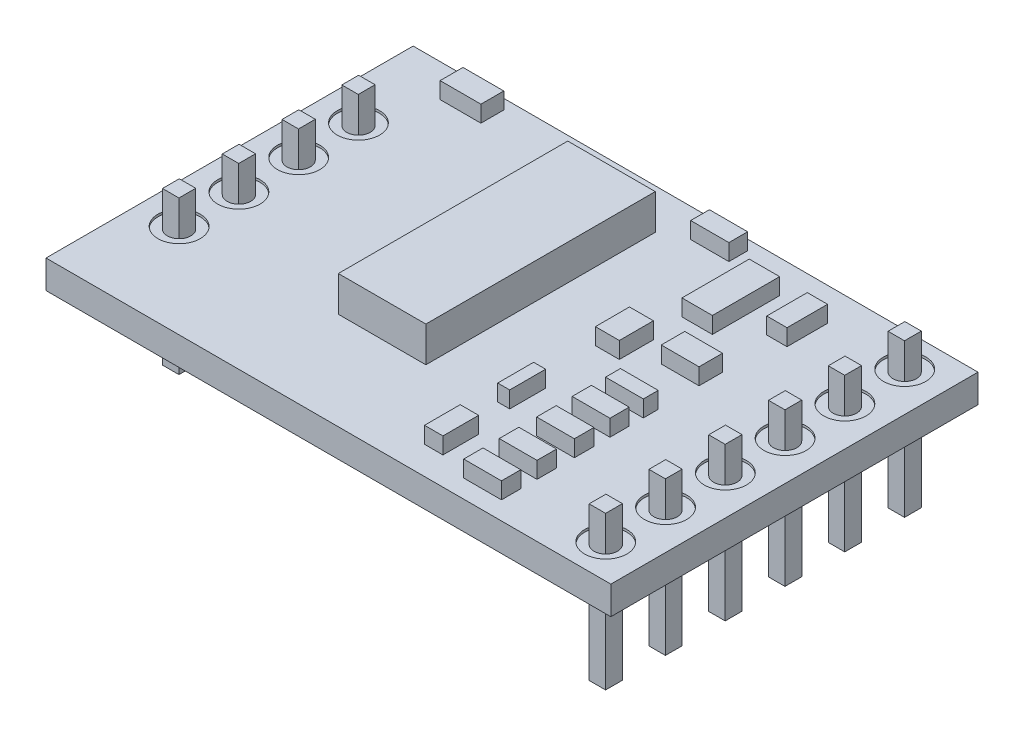
SolidWorks part; units mm, degrees
ref_plane "Front Plane" through (0, 0, 0) normal (0, 0, 1) x (1, 0, 0)
ref_plane "Top Plane" through (0, 0, 0) normal (0, 1, 0) x (1, 0, 0)
ref_plane "Right Plane" through (0, 0, 0) normal (1, 0, 0) x (0, 0, -1)
sketch "Sketch1" plane through (0, 0, 0) normal (0, 1, 0) x (1, 0, 0)
  line L1 (-12, -7.8) -> (12, -7.8)
  line L2 (-12, -7.8) -> (-12, 7.8)
  line L3 (-12, 7.8) -> (12, 7.8)
  line L4 (12, -7.8) -> (12, 7.8)
  line L5 (-12, -7.8) -> (12, 7.8) construction
  line L6 (-12, 7.8) -> (12, -7.8) construction
  point P0 (0, 0)
  dimension "D1" = 24
  dimension "D2" = 15.6
extrude "Boss-Extrude1" add sketch "Sketch1" along normal blind 1.2
sketch "Sketch3" plane through (0, 1.2, 0) normal (0, 1, 0) x (1, 0, 0)
  line L1 (-3.7188, 6.0872) -> (0, 6.0872)
  line L2 (-3.7188, 6.0872) -> (-3.7188, -3.6601)
  line L3 (-3.7188, -3.6601) -> (0, -3.6601)
  line L4 (0, 6.0872) -> (0, -3.6601)
extrude "Boss-Extrude2" add sketch "Sketch3" along normal blind 1.5
sketch "Sketch4" plane through (0, 1.2, 0) normal (0, 1, 0) x (1, 0, 0)
  line L1 (3.6797, 6.4003) -> (4.9715, 6.4003)
  line L2 (3.6797, 6.4003) -> (3.6797, 3.5427)
  line L3 (3.6797, 3.5427) -> (4.9715, 3.5427)
  line L4 (4.9715, 6.4003) -> (4.9715, 3.5427)
  line L5 (6.1459, 6.4003) -> (7.0071, 6.4003)
  line L6 (6.1459, 6.4003) -> (6.1459, 4.6779)
  line L7 (6.1459, 4.6779) -> (7.0071, 4.6779)
  line L8 (7.0071, 6.4003) -> (7.0071, 4.6779)
  line L9 (2.8968, 2.0943) -> (3.9146, 2.0943)
  line L10 (2.8968, 2.0943) -> (2.8968, 0.6459)
  line L11 (2.8968, 0.6459) -> (3.9146, 0.6459)
  line L12 (3.9146, 2.0943) -> (3.9146, 0.6459)
  line L13 (4.9715, 2.3683) -> (6.5765, 2.3683)
  line L14 (4.9715, 2.3683) -> (4.9715, 1.3701)
  line L15 (4.9715, 1.3701) -> (6.5765, 1.3701)
  line L16 (6.5765, 2.3683) -> (6.5765, 1.3701)
  line L17 (2.8968, -1.9769) -> (3.4057, -1.9769)
  line L18 (2.8968, -1.9769) -> (2.8968, -3.5035)
  line L19 (2.8968, -3.5035) -> (3.4057, -3.5035)
  line L20 (3.4057, -1.9769) -> (3.4057, -3.5035)
  line L21 (4.9715, -0.3642) -> (6.5765, -0.3642)
  line L22 (4.9715, -0.3642) -> (4.9715, -0.9964)
  line L23 (4.9715, -0.9964) -> (6.5765, -0.9964)
  line L24 (6.5765, -0.3642) -> (6.5765, -0.9964)
  line L25 (4.9715, -1.5977) -> (6.5765, -1.5977)
  line L26 (4.9715, -1.5977) -> (4.9715, -2.415)
  line L27 (4.9715, -2.415) -> (6.5765, -2.415)
  line L28 (6.5765, -1.5977) -> (6.5765, -2.415)
  line L29 (4.9715, -3.0934) -> (6.5765, -3.0934)
  line L30 (4.9715, -3.0934) -> (4.9715, -3.9261)
  line L31 (4.9715, -3.9261) -> (6.5765, -3.9261)
  line L32 (6.5765, -3.0934) -> (6.5765, -3.9261)
  line L33 (4.9715, -4.6817) -> (6.5765, -4.6817)
  line L34 (4.9715, -4.6817) -> (4.9715, -5.5143)
  line L35 (4.9715, -5.5143) -> (6.5765, -5.5143)
  line L36 (6.5765, -4.6817) -> (6.5765, -5.5143)
  line L37 (4.9715, -6.2045) -> (6.5765, -6.2045)
  line L38 (4.9715, -6.2045) -> (4.9715, -7.0239)
  line L39 (4.9715, -7.0239) -> (6.5765, -7.0239)
  line L40 (6.5765, -6.2045) -> (6.5765, -7.0239)
  line L41 (2.8968, -5.098) -> (3.6797, -5.098)
  line L42 (2.8968, -5.098) -> (2.8968, -6.6142)
  line L43 (2.8968, -6.6142) -> (3.6797, -6.6142)
  line L44 (3.6797, -5.098) -> (3.6797, -6.6142)
  line L45 (1.0168, 7.3718) -> (2.6398, 7.3718)
  line L46 (1.0168, 7.3718) -> (1.0168, 6.575)
  line L47 (1.0168, 6.575) -> (2.6398, 6.575)
  line L48 (2.6398, 7.3718) -> (2.6398, 6.575)
  line L49 (-9.4546, 7.3718) -> (-7.7209, 7.3718)
  line L50 (-9.4546, 7.3718) -> (-9.4546, 6.4003)
  line L51 (-9.4546, 6.4003) -> (-7.7209, 6.4003)
  line L52 (-7.7209, 7.3718) -> (-7.7209, 6.4003)
extrude "Boss-Extrude3" add sketch "Sketch4" along normal blind 0.7
sketch "Sketch5" plane through (0, 1.2, 0) normal (0, 1, 0) x (1, 0, 0)
  line L0 (-10.3345, 7.8) -> (-10.3345, -7.8) construction
  line L1 (12, 7.8) -> (-12, 7.8) construction
  line L2 (-12, -7.8) -> (12, -7.8) construction
  line L3 (0, 0) -> (0, -7.8) construction
  circle A0 centre (-10.3345, 3.81) radius 0.5
  circle A1 centre (-10.3345, 1.27) radius 0.5
  circle A2 centre (-10.3345, -1.27) radius 0.5
  circle A3 centre (-10.3345, -3.81) radius 0.5
  circle A4 centre (10.3345, -3.81) radius 0.5
  circle A5 centre (10.3345, -1.27) radius 0.5
  circle A6 centre (10.3345, 1.27) radius 0.5
  circle A7 centre (10.3345, 3.81) radius 0.5
  circle A8 centre (10.3345, 6.35) radius 0.5
  circle A9 centre (10.3345, -6.35) radius 0.5
  dimension "D2" = 1
  dimension "D1" = 3.99
  dimension "D4" = 2
  dimension "D3" = 4
  dimension "D5" = 2
extrude "Cut-Extrude1" cut sketch "Sketch5" against normal through all
sketch "Sketch6" plane through (0, 1.2, 0) normal (0, 1, 0) x (1, 0, 0)
  circle A0 centre (-10.3345, 3.81) radius 0.9
  circle A1 centre (-10.3345, 1.27) radius 0.9
  circle A2 centre (-10.3345, -1.27) radius 0.9
  circle A3 centre (-10.3345, -3.81) radius 0.9
  dimension "D1" = 1.8
  dimension "D2" = 4
extrude "Cut-Extrude2" cut sketch "Sketch6" against normal blind 0.1
sketch "Sketch7" plane through (0, 1.2, 0) normal (0, 1, 0) x (1, 0, 0)
  circle A0 centre (10.3345, 6.35) radius 0.9
  circle A1 centre (10.3345, 3.81) radius 0.9
  circle A2 centre (10.3345, 1.27) radius 0.9
  circle A3 centre (10.3345, -1.27) radius 0.9
  circle A4 centre (10.3345, -3.81) radius 0.9
  circle A5 centre (10.3345, -6.35) radius 0.9
  dimension "D1" = 1.8
  dimension "D2" = 6
extrude "Cut-Extrude3" cut sketch "Sketch7" against normal blind 0.1
sketch "Sketch8" plane through (0, 1.1, 0) normal (0, 1, 0) x (1, 0, 0)
  line L0 (-10.6845, 0.9129) -> (-9.9845, 0.9129)
  line L1 (-10.6845, 3.4529) -> (-9.9845, 3.4529)
  line L2 (-10.6845, 3.4529) -> (-10.6845, 4.1671)
  line L3 (-10.6845, 4.1671) -> (-9.9845, 4.1671)
  line L4 (-9.9845, 3.4529) -> (-9.9845, 4.1671)
  line L5 (-10.6845, 3.4529) -> (-9.9845, 4.1671) construction
  line L6 (-10.6845, 4.1671) -> (-9.9845, 3.4529) construction
  line L7 (-10.6845, 0.9129) -> (-10.6845, 1.6271)
  line L8 (-10.6845, 1.6271) -> (-9.9845, 1.6271)
  line L9 (-9.9845, 0.9129) -> (-9.9845, 1.6271)
  line L10 (-10.6845, 0.9129) -> (-9.9845, 1.6271) construction
  line L11 (-10.6845, 1.6271) -> (-9.9845, 0.9129) construction
  line L12 (-10.6845, -1.6271) -> (-9.9845, -1.6271)
  line L13 (-10.6845, -1.6271) -> (-10.6845, -0.9129)
  line L14 (-10.6845, -0.9129) -> (-9.9845, -0.9129)
  line L15 (-9.9845, -1.6271) -> (-9.9845, -0.9129)
  line L16 (-10.6845, -1.6271) -> (-9.9845, -0.9129) construction
  line L17 (-10.6845, -0.9129) -> (-9.9845, -1.6271) construction
  line L18 (-10.6845, -4.1671) -> (-9.9845, -4.1671)
  line L19 (-10.6845, -4.1671) -> (-10.6845, -3.4529)
  line L20 (-10.6845, -3.4529) -> (-9.9845, -3.4529)
  line L21 (-9.9845, -4.1671) -> (-9.9845, -3.4529)
  line L22 (-10.6845, -4.1671) -> (-9.9845, -3.4529) construction
  line L23 (-10.6845, -3.4529) -> (-9.9845, -4.1671) construction
  line L24 (0, 0) -> (0, -7.8) construction
  line L25 (-12, -7.8) -> (12, -7.8) construction
  line L26 (10.6845, -3.4529) -> (9.9845, -4.1671) construction
  line L27 (10.6845, -4.1671) -> (9.9845, -3.4529) construction
  line L28 (10.6845, -0.9129) -> (9.9845, -1.6271) construction
  line L29 (10.6845, -1.6271) -> (9.9845, -0.9129) construction
  line L30 (10.6845, 1.6271) -> (9.9845, 0.9129) construction
  line L31 (10.6845, 0.9129) -> (9.9845, 1.6271) construction
  line L32 (10.6845, 4.1671) -> (9.9845, 3.4529) construction
  line L33 (10.6845, 3.4529) -> (9.9845, 4.1671) construction
  line L34 (9.9845, -4.1671) -> (9.9845, -3.4529)
  line L35 (10.6845, -3.4529) -> (9.9845, -3.4529)
  line L36 (10.6845, -4.1671) -> (10.6845, -3.4529)
  line L37 (10.6845, -4.1671) -> (9.9845, -4.1671)
  line L38 (9.9845, -1.6271) -> (9.9845, -0.9129)
  line L39 (10.6845, -0.9129) -> (9.9845, -0.9129)
  line L40 (10.6845, -1.6271) -> (10.6845, -0.9129)
  line L41 (10.6845, -1.6271) -> (9.9845, -1.6271)
  line L42 (9.9845, 0.9129) -> (9.9845, 1.6271)
  line L43 (10.6845, 1.6271) -> (9.9845, 1.6271)
  line L44 (10.6845, 0.9129) -> (10.6845, 1.6271)
  line L45 (9.9845, 3.4529) -> (9.9845, 4.1671)
  line L46 (10.6845, 4.1671) -> (9.9845, 4.1671)
  line L47 (10.6845, 3.4529) -> (10.6845, 4.1671)
  line L48 (10.6845, 3.4529) -> (9.9845, 3.4529)
  line L49 (10.6845, 0.9129) -> (9.9845, 0.9129)
  line L50 (9.9845, 5.9929) -> (9.9845, 6.7071)
  line L51 (10.6845, 6.7071) -> (9.9845, 6.7071)
  line L52 (10.6845, 5.9929) -> (10.6845, 6.7071)
  line L53 (10.6845, 5.9929) -> (9.9845, 5.9929)
  line L54 (10.6845, 6.7071) -> (9.9845, 5.9929) construction
  line L55 (10.6845, 5.9929) -> (9.9845, 6.7071) construction
  line L56 (9.9845, -6.7071) -> (9.9845, -5.9929)
  line L57 (10.6845, -5.9929) -> (9.9845, -5.9929)
  line L58 (10.6845, -6.7071) -> (10.6845, -5.9929)
  line L59 (10.6845, -6.7071) -> (9.9845, -6.7071)
  line L60 (10.6845, -5.9929) -> (9.9845, -6.7071) construction
  line L61 (10.6845, -6.7071) -> (9.9845, -5.9929) construction
  circle A0 centre (-10.3345, 3.81) radius 0.5 construction
  point P0 (-10.3345, 3.81)
  point P9 (-10.3345, 1.27)
  point P14 (-10.3345, -1.27)
  point P19 (-10.3345, -3.81)
  point P44 (10.3345, -3.81)
  point P45 (10.3345, -1.27)
  point P46 (10.3345, 1.27)
  point P47 (10.3345, 3.81)
  point P53 (10.3345, 6.35)
  point P58 (10.3345, -6.35)
  dimension "D1" = 0.7
  dimension "D2" = 0.7141
  dimension "D3" = 4
  dimension "D4" = 2
  dimension "D5" = 2
extrude "Boss-Extrude5" add sketch "Sketch8" against normal blind 5 and the other way blind 1.5 separate body
